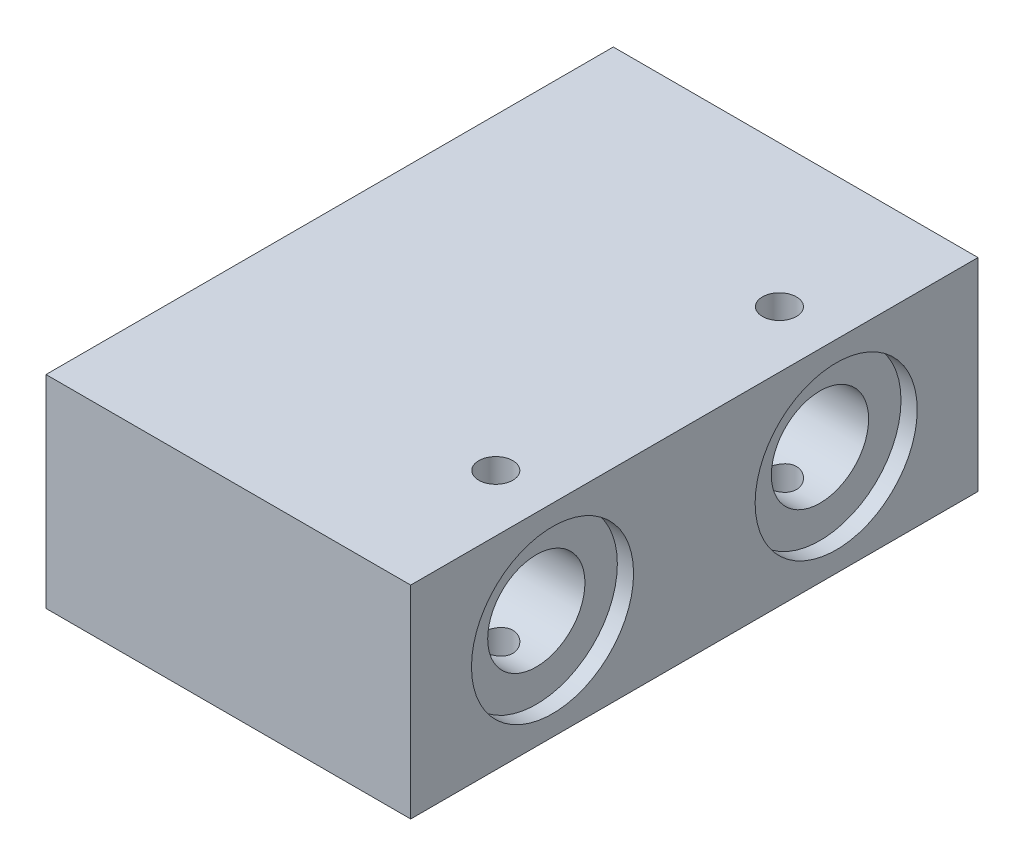
SolidWorks part; units mm, degrees
ref_plane "Front Plane" through (0, 0, 0) normal (0, 0, 1) x (1, 0, 0)
ref_plane "Top Plane" through (0, 0, 0) normal (0, 1, 0) x (1, 0, 0)
ref_plane "Right Plane" through (0, 0, 0) normal (1, 0, 0) x (0, 0, -1)
sketch "Sketch1" plane through (0, 0, 0) normal (0, 1, 0) x (1, 0, 0)
  line L1 (-22.5, -51) -> (22.5, -51)
  line L2 (-22.5, -51) -> (-22.5, 51)
  line L3 (-22.5, 51) -> (22.5, 51)
  line L4 (22.5, -51) -> (22.5, 51)
  line L5 (-22.5, -51) -> (22.5, 51) construction
  line L6 (-22.5, 51) -> (22.5, -51) construction
  point P0 (0, 0)
  dimension "D1" = 45
  dimension "D2" = 102
extrude "Boss-Extrude1" add sketch "Sketch1" along normal blind 25
hole_wizard "M5 Tapped Hole3" positions "Sketch12" profile "Sketch13" tap size "M5" standard "DIN" end condition through all
sketch "Sketch12" plane through (0, 25, 0) normal (0, 1, 0) x (1, 0, 0)
  line L0 (22.5, -51) -> (22.5, 51) construction
  line L1 (-22.5, -51) -> (22.5, -51) construction
  point P0 (15.5, 17.5)
  point P2 (15.5, -17.5)
  dimension "D1" = 7
  dimension "D2" = 7
  dimension "D3" = 33.5
  dimension "D4" = 35
sketch "Sketch13" plane through (15.5, 25, -17.5) normal (1, 0, 0) x (0, 0, 1)
  line L0 (0, 0) -> (0, 25)
  line L1 (0, 25) -> (2.1, 25)
  line L2 (2.1, 25) -> (2.1, 0)
  line L5 (2.1, 0) -> (0, 0)
  line L11 (0, -6.35) -> (0, 107.95) construction
  dimension "Thru Tap Drill Dia." = 4.2
  dimension "Thru Tap Drill Depth" = 25
cosmetic thread "Hole Thread9" parameters "D2"=5
cosmetic thread "Hole Thread10" parameters "D2"=5
sketch "Sketch27" plane through (-22.5, 0, 0) normal (-1, 0, 0) x (0, 0, 1)
  line L0 (51, 25) -> (51, 0) construction
  line L1 (-51, 25) -> (51, 25) construction
  circle A0 centre (-17.5, 12.5) radius 6
  circle A1 centre (17.5, 12.5) radius 6
  dimension "D1" = 12
  dimension "D2" = 12
  dimension "D5" = 12.5
  dimension "D3" = 33.5
  dimension "D4" = 35
  dimension "D6" = 12.5
extrude "Cut-Extrude1" cut sketch "Sketch27" against normal blind 74
sketch "Sketch28" plane through (-22.5, 0, 0) normal (-1, 0, 0) x (0, 0, 1)
  circle A0 centre (-17.5, 12.5) radius 10
  circle A1 centre (17.5, 12.5) radius 10
  dimension "D1" = 20
  dimension "D2" = 20
extrude "Cut-Extrude3" cut sketch "Sketch28" against normal blind 2
sketch "Sketch30" plane through (22.5, 0, 0) normal (1, 0, 0) x (0, 0, -1)
  circle A0 centre (-17.5, 12.5) radius 10
  circle A1 centre (17.5, 12.5) radius 10
  dimension "D1" = 20
  dimension "D2" = 20
extrude "Cut-Extrude4" cut sketch "Sketch30" against normal blind 2
hole_wizard "M5 Tapped Hole4" positions "Sketch31" profile "Sketch32" tap size "M5" standard "DIN"
sketch "Sketch31" plane through (0, 0, -51) normal (0, 0, -1) x (-1, 0, 0)
  line L0 (22.5, 25) -> (22.5, 0) construction
  line L1 (-22.5, 25) -> (-22.5, 0) construction
  line L3 (-22.5, 0) -> (22.5, 0) construction
  line L4 (-22.5, 25) -> (22.5, 25) construction
  point P0 (-18, 5)
  point P2 (18, 20)
  dimension "D1" = 4.5
  dimension "D2" = 4.5
  dimension "D3" = 5
  dimension "D4" = 5
sketch "Sketch32" plane through (18, 5, -51) normal (1, 0, 0) x (0, 1, 0)
  line L0 (0, 0) -> (0, 15.2618)
  line L1 (0, 15.2618) -> (2.1, 14)
  line L2 (2.1, 14) -> (2.1, 0)
  line L5 (2.1, 0) -> (0, 0)
  line L10 (0, 15.2618) -> (-2.1, 14) construction
  line L11 (0, -6.35) -> (0, 107.95) construction
  dimension "Tap Drill Dia." = 4.2
  dimension "Tap Drill Depth" = 14
  dimension "Drill Angle" = 118
cosmetic thread "Hole Thread11" parameters "D1"=10, "D2"=5
cosmetic thread "Hole Thread12" parameters "D1"=10, "D2"=5
hole_wizard "M5 Tapped Hole5" positions "Sketch33" profile "Sketch34" tap size "M5" standard "DIN"
sketch "Sketch33" plane through (-22.5, 0, 0) normal (-1, 0, 0) x (0, 0, 1)
  line L0 (-51, 0) -> (51, 0) construction
  point P0 (0, 12.5)
  dimension "D1" = 12.5
sketch "Sketch34" plane through (-22.5, 12.5, 0) normal (0, 1, 0) x (0, 0, 1)
  line L0 (0, 0) -> (0, 16.2618)
  line L1 (0, 16.2618) -> (2.1, 15)
  line L2 (2.1, 15) -> (2.1, 0)
  line L5 (2.1, 0) -> (0, 0)
  line L10 (0, 16.2618) -> (-2.1, 15) construction
  line L11 (0, -6.35) -> (0, 107.95) construction
  dimension "Tap Drill Dia." = 4.2
  dimension "Tap Drill Depth" = 15
  dimension "Drill Angle" = 118
cosmetic thread "Hole Thread13" parameters "D1"=10, "D2"=5
sketch "Sketch37" plane through (0, 25, 0) normal (0, 1, 0) x (1, 0, 0)
  line L0 (-22.5, 35) -> (22.5, 35)
  line L1 (-22.5, 51) -> (-22.5, -51) construction
  line L2 (22.5, -51) -> (22.5, 51) construction
  line L3 (22.5, 51) -> (-22.5, 51) construction
  dimension "D1" = 16
extrude "Cut-Extrude5" cut sketch "Sketch37" against normal through all and the other way through all
sketch "Sketch38" plane through (0, 25, 0) normal (0, 1, 0) x (1, 0, 0)
  line L0 (-22.5, -35) -> (22.5, -35)
  line L1 (-22.5, 35) -> (-22.5, -51) construction
  line L2 (22.5, -51) -> (22.5, 35) construction
  line L3 (-22.5, -51) -> (22.5, -51) construction
  dimension "D1" = 16
extrude "Cut-Extrude12" cut sketch "Sketch38" against normal through all and the other way through all flip side to cut
hole_wizard "M5 Tapped Hole6" positions "Sketch39" profile "Sketch40" tap size "M5" standard "DIN"
sketch "Sketch39" plane through (-22.5, 0, 0) normal (-1, 0, 0) x (0, 0, 1)
  line L1 (-35, 25) -> (-35, 0) construction
  line L2 (35, 25) -> (35, 0) construction
  point P0 (-29, 5)
  point P2 (29, 20)
  dimension "D1" = 6
  dimension "D2" = 7.5
  dimension "D3" = 6
  dimension "D4" = 7.5
sketch "Sketch40" plane through (-22.5, 5, -29) normal (0, 1, 0) x (0, 0, 1)
  line L0 (0, 0) -> (0, 16.2618)
  line L1 (0, 16.2618) -> (2.1, 15)
  line L2 (2.1, 15) -> (2.1, 0)
  line L5 (2.1, 0) -> (0, 0)
  line L10 (0, 16.2618) -> (-2.1, 15) construction
  line L11 (0, -6.35) -> (0, 107.95) construction
  dimension "Tap Drill Dia." = 4.2
  dimension "Tap Drill Depth" = 15
  dimension "Drill Angle" = 118
cosmetic thread "Hole Thread14" parameters "D1"=10, "D2"=5
cosmetic thread "Hole Thread15" parameters "D1"=10, "D2"=5
